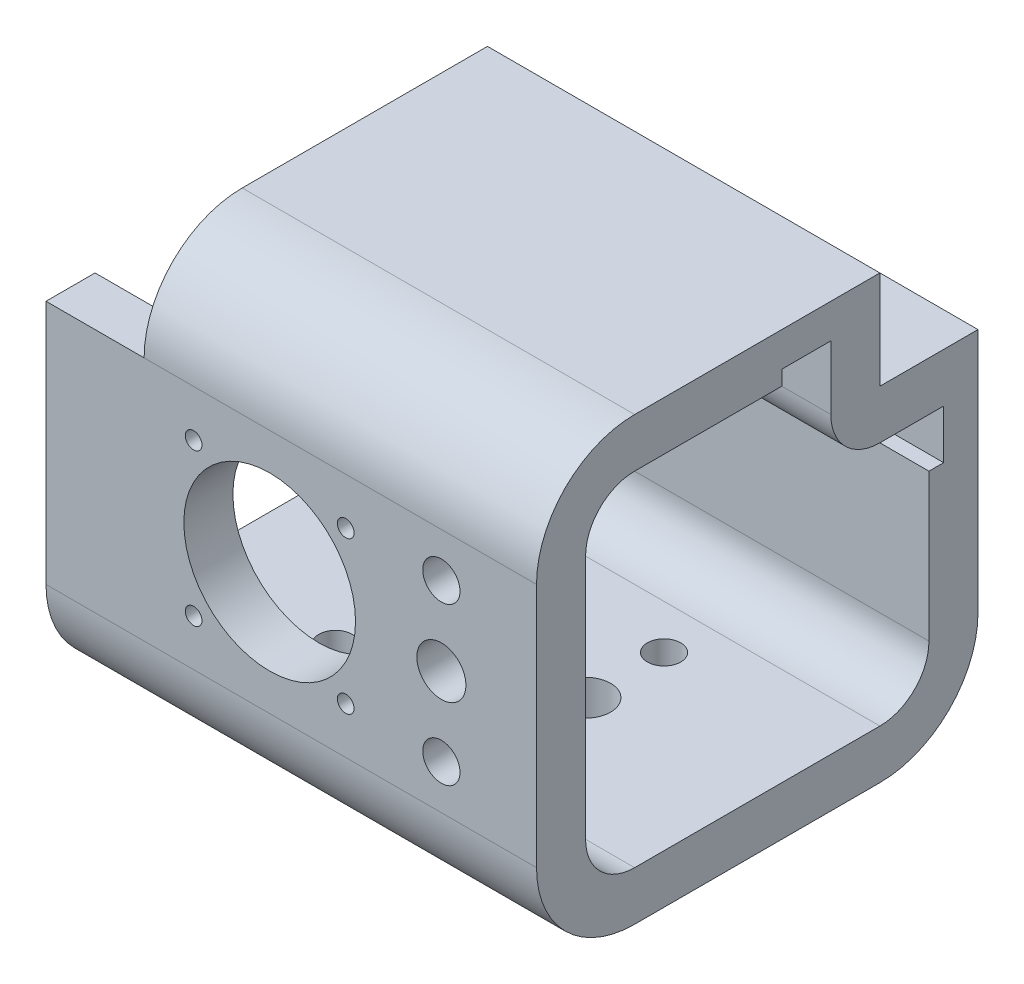
SolidWorks part; units mm, degrees
material "ABS"
ref_plane "Front Plane" through (0, 0, 0) normal (0, 0, 1) x (1, 0, 0)
ref_plane "Top Plane" through (0, 0, 0) normal (0, 1, 0) x (1, 0, 0)
ref_plane "Right Plane" through (0, 0, 0) normal (1, 0, 0) x (0, 0, -1)
sketch "Sketch2" plane through (0, 0, 0) normal (1, 0, 0) x (0, 0, -1)
  line L0 (-420.8016, -665) -> (-420.8016, -615) construction
  line L1 (-30.8, 35.0024) -> (19.2, 35.0024)
  line L2 (-40.8, 25.0024) -> (-40.8, -24.9976)
  line L3 (-30.8, -34.9976) -> (19.2, -34.9976)
  line L4 (29.2, 25.0024) -> (29.2, -24.9976)
  line L7 (-30.8, -44.9976) -> (19.2, -44.9976)
  line L8 (39.2, 25.0024) -> (39.2, -24.9976)
  line L9 (-30.8, 45.0024) -> (19.2, 45.0024)
  line L10 (-50.8, 25.0024) -> (-50.8, -24.9976)
  line L12 (19.1969, 45.0024) -> (-480.8031, 45.0024) construction
  line L13 (-40.8, 16.3216) -> (-40.8, -16.3216) construction
  arc A0 (-30.8, 35.0024) -> (-40.8, 25.0024) centre (-30.8, 25.0024) ccw
  arc A1 (19.2, 35.0024) -> (29.2, 25.0024) centre (19.2, 25.0024) cw
  arc A2 (19.2, -34.9976) -> (29.2, -24.9976) centre (19.2, -24.9976) ccw
  arc A3 (-40.8, -24.9976) -> (-30.8, -34.9976) centre (-30.8, -24.9976) ccw
  arc A4 (19.2, -44.9976) -> (39.2, -24.9976) centre (19.2, -24.9976) ccw
  arc A5 (19.2, 45.0024) -> (39.2, 25.0024) centre (19.2, 25.0024) cw
  arc A6 (-30.8, 45.0024) -> (-50.8, 25.0024) centre (-30.8, 25.0024) ccw
  arc A7 (-50.8, -24.9976) -> (-30.8, -44.9976) centre (-30.8, -24.9976) ccw
  dimension "D1" = 10
  dimension "D2" = 10
extrude "Boss-Extrude1" add sketch "Sketch2" along normal up to surface (54.4 mm away) and the other way up to surface (45.6 mm away)
sketch "Sketch3" plane through (0, 0, 50.8) normal (0, 0, 1) x (1, 0, 0)
  circle A0 centre (35, -16) radius 3.8 construction
  circle A1 centre (35, 0) radius 5 construction
  circle A2 centre (35, 16) radius 3.8 construction
  circle A3 centre (35, -16) radius 3.8
  circle A4 centre (35, 0) radius 5
  circle A5 centre (35, 16) radius 3.8
  arc A6 (-5.2807, -14.0397) -> (-6.2044, -13.6567) centre (0, 0) ccw construction
  circle A7 centre (0, 0) radius 15 construction
  circle A8 centre (0, 0) radius 17.5
  circle A9 centre (15.5, 15.5) radius 1.7 construction
  circle A10 centre (15.5, -15.5) radius 1.7 construction
  circle A11 centre (-15.5, 15.5) radius 1.7 construction
  circle A12 centre (-15.5, -15.5) radius 1.7 construction
  circle A13 centre (15.5, 15.5) radius 1.7
  circle A14 centre (15.5, -15.5) radius 1.7
  circle A15 centre (-15.5, 15.5) radius 1.7
  circle A16 centre (-15.5, -15.5) radius 1.7
  dimension "D1" = 2.5
extrude "Cut-Extrude1" cut sketch "Sketch3" against normal up to next
sketch "Sketch4" plane through (0, -44.9976, 0) normal (0, -1, 0) x (1, 0, 0)
  line L0 (-45.6, 5.8) -> (54.4, 5.8) construction
  line L1 (-15.6, -508.7016) -> (-15.6, 49491.2984) construction
  line L2 (-45.6, 30.8) -> (-45.6, -19.2) construction
  line L3 (54.4, -19.2) -> (54.4, 30.8) construction
  line L4 (19.4, -508.7016) -> (19.4, 49491.2984) construction
  circle A0 centre (-15.6, 5.8) radius 5.1
  circle A1 centre (19.4, 5.8) radius 5.1
  circle A4 centre (19.4, 455.8016) radius 5.1 construction
  circle A5 centre (-15.6, 21.8) radius 3.4 construction
  circle A6 centre (-15.6, -10.2) radius 3.4 construction
  circle A7 centre (19.4, 21.8) radius 3.4 construction
  circle A8 centre (19.4, -10.2) radius 3.4 construction
  circle A9 centre (-15.6, 21.8) radius 3.4
  circle A10 centre (-15.6, -10.2) radius 3.4
  circle A11 centre (19.4, 21.8) radius 3.4
  circle A12 centre (19.4, -10.2) radius 3.4
extrude "Cut-Extrude2" cut sketch "Sketch4" against normal up to next
sketch "Sketch6" plane through (0, 0, -39.2) normal (0, 0, -1) x (-1, 0, 0)
  line L0 (45.6, -24.9976) -> (45.6, 25.0024) construction
  line L1 (45.6, 45.0024) -> (25.6, 45.0024)
  line L2 (45.6, 45.0024) -> (45.6, 25.0024)
  line L3 (45.6, 25.0024) -> (25.6, 25.0024)
  line L4 (25.6, 45.0024) -> (25.6, 25.0024)
  line L5 (-54.4, 45.0024) -> (45.6, 45.0024) construction
  dimension "D1" = 20
extrude "Cut-Extrude4" cut sketch "Sketch6" against normal through all
sketch "Sketch7" plane through (0, -44.9976, 0) normal (0, -1, 0) x (1, 0, 0)
  line L0 (-45.6, 30.8) -> (-45.6, -19.2) construction
  line L1 (-45.6, -39.2) -> (-25.6, -39.2)
  line L2 (-45.6, -39.2) -> (-45.6, -19.2)
  line L3 (-45.6, -19.2) -> (-25.6, -19.2)
  line L4 (-25.6, -39.2) -> (-25.6, -19.2)
  line L5 (54.4, -39.2) -> (-45.6, -39.2) construction
  dimension "D1" = 20
extrude "Cut-Extrude5" cut sketch "Sketch7" against normal through all
sketch "Sketch5" plane through (-45.6, 0, 0) normal (-1, 0, 0) x (0, 0, 1)
  line L0 (-39.2, -24.9976) -> (-39.2, 25.0024) construction
  line L1 (-19.2, 25.0024) -> (-39.2, 25.0024)
  line L2 (-19.2, 25.0024) -> (-19.2, 45.0024)
  line L3 (-19.2, 45.0024) -> (-39.2, 45.0024)
  line L4 (-39.2, 25.0024) -> (-39.2, 45.0024)
  line L5 (-19.2, 45.0024) -> (30.8, 45.0024) construction
  line L6 (-29.2, -24.9976) -> (-29.2, 25.0024) construction
  line L7 (-32.2, 25.0024) -> (-29.2, 25.0024)
  line L8 (-32.2, 25.0024) -> (-32.2, 5.0024)
  line L9 (-32.2, 5.0024) -> (-29.2, 5.0024)
  line L10 (-29.2, 25.0024) -> (-29.2, 5.0024)
  line L11 (-19.2, 35.0024) -> (30.8, 35.0024) construction
  line L12 (-19.2, 38.0024) -> (0.8, 38.0024)
  line L13 (-19.2, 38.0024) -> (-19.2, 35.0024)
  line L14 (-19.2, 35.0024) -> (0.8, 35.0024)
  line L15 (0.8, 38.0024) -> (0.8, 35.0024)
  line L16 (460.8016, -675) -> (480.8016, -675) construction
  line L17 (460.8016, -675) -> (460.8016, -678) construction
  dimension "D1" = 20
extrude "Cut-Extrude3" cut sketch "Sketch5" against normal through all
sketch "Sketch8" plane through (-25.6, 0, 0) normal (-1, 0, 0) x (0, 0, 1)
  line L0 (-19.2, 38.0024) -> (-19.2, 25.0024)
  line L1 (-32.2, 25.0024) -> (-19.2, 25.0024)
  line L2 (-9.2, 38.0024) -> (-9.2, 25.0024)
  line L3 (-32.2, 15.0024) -> (-19.2, 15.0024)
  line L4 (-9.2, 38.0024) -> (-9.2, 15.0024) construction
  line L5 (-32.2, 15.0024) -> (-9.2, 15.0024) construction
  line L6 (-9.2, 38.0024) -> (-19.2, 38.0024)
  line L7 (-32.2, 25.0024) -> (-32.2, 15.0024)
  arc A0 (-9.2, 25.0024) -> (-19.2, 15.0024) centre (-19.2, 25.0024) cw
  dimension "D2" = 10
  dimension "D1" = 10
extrude "Boss-Extrude2" add sketch "Sketch8" against normal up to surface (80 mm away) up to face at (54.4, 3.9917, 1.8107)
